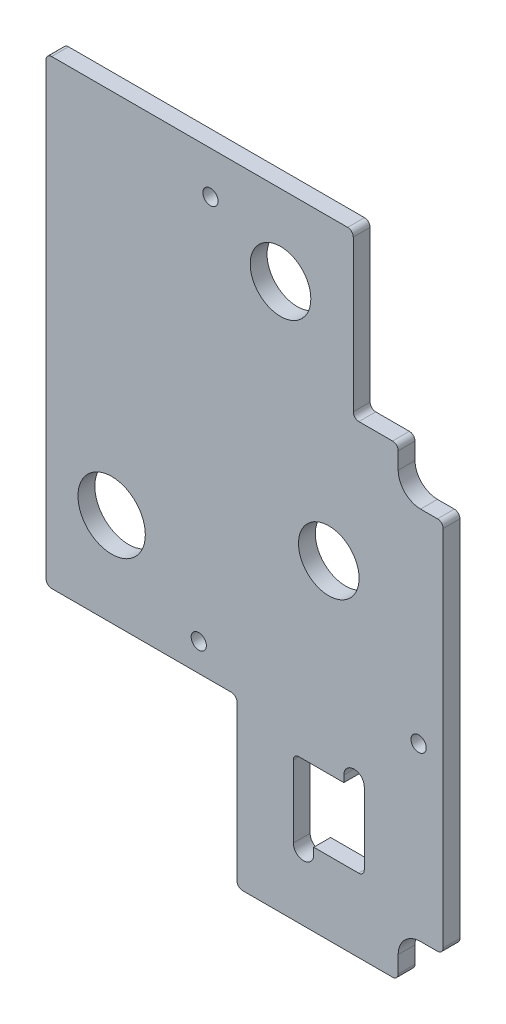
SolidWorks part; units mm, degrees
ref_plane "Front Plane" through (0, 0, 0) normal (0, 0, 1) x (1, 0, 0)
ref_plane "Top Plane" through (0, 0, 0) normal (0, 1, 0) x (1, 0, 0)
ref_plane "Right Plane" through (0, 0, 0) normal (1, 0, 0) x (0, 0, -1)
sketch "Sketch3" plane through (0, 0, 0) normal (0, 0, 1) x (1, 0, 0)
  line L8 (13.7795, -148.717) -> (13.7795, -168.783)
  line L9 (33.8455, -148.717) -> (13.7795, -148.717)
  line L10 (33.8455, -168.783) -> (33.8455, -148.717)
  line L11 (13.7795, -168.783) -> (33.8455, -168.783)
  line L12 (-0.5715, -189.484) -> (41.8465, -189.484)
  line L13 (43.434, -187.8965) -> (43.434, -183.134)
  line L14 (49.784, -176.784) -> (54.5465, -176.784)
  line L15 (56.134, -175.1965) -> (56.134, -72.4535)
  line L16 (54.5465, -70.866) -> (49.784, -70.866)
  line L17 (43.434, -64.516) -> (43.434, -59.7535)
  line L18 (41.8465, -58.166) -> (32.3215, -58.166)
  line L19 (30.734, -56.5785) -> (30.734, -13.7795)
  line L20 (29.1465, -12.192) -> (-54.5465, -12.192)
  line L21 (-56.134, -13.7795) -> (-56.134, -140.9065)
  line L22 (-54.5465, -142.494) -> (-3.7465, -142.494)
  line L23 (-2.159, -144.0815) -> (-2.159, -187.8965)
  line L24 (-0.5715, -189.484) -> (41.8465, -189.484)
  line L25 (43.434, -187.8965) -> (43.434, -183.134)
  line L26 (49.784, -176.784) -> (54.5465, -176.784)
  line L27 (56.134, -175.1965) -> (56.134, -72.4535)
  line L28 (54.5465, -70.866) -> (49.784, -70.866)
  line L29 (43.434, -64.516) -> (43.434, -59.7535)
  line L30 (41.8465, -58.166) -> (32.3215, -58.166)
  line L31 (30.734, -56.5785) -> (30.734, -13.7795)
  line L32 (29.1465, -12.192) -> (-54.5465, -12.192)
  line L33 (-56.134, -13.7795) -> (-56.134, -140.9065)
  line L34 (-54.5465, -142.494) -> (-3.7465, -142.494)
  line L35 (-2.159, -144.0815) -> (-2.159, -187.8965)
  arc A12 (-2.159, -187.8965) -> (-0.5715, -189.484) centre (-0.5715, -187.8965) ccw
  arc A13 (-2.159, -187.8965) -> (-0.5715, -189.484) centre (-0.5715, -187.8965) ccw
  arc A14 (41.8465, -189.484) -> (43.434, -187.8965) centre (41.8465, -187.8965) ccw
  arc A15 (41.8465, -189.484) -> (43.434, -187.8965) centre (41.8465, -187.8965) ccw
  arc A16 (49.784, -176.784) -> (43.434, -183.134) centre (49.784, -183.134) ccw
  arc A17 (49.784, -176.784) -> (43.434, -183.134) centre (49.784, -183.134) ccw
  arc A18 (54.5465, -176.784) -> (56.134, -175.1965) centre (54.5465, -175.1965) ccw
  arc A19 (54.5465, -176.784) -> (56.134, -175.1965) centre (54.5465, -175.1965) ccw
  arc A20 (56.134, -72.4535) -> (54.5465, -70.866) centre (54.5465, -72.4535) ccw
  arc A21 (56.134, -72.4535) -> (54.5465, -70.866) centre (54.5465, -72.4535) ccw
  arc A22 (43.434, -64.516) -> (49.784, -70.866) centre (49.784, -64.516) ccw
  arc A23 (43.434, -64.516) -> (49.784, -70.866) centre (49.784, -64.516) ccw
  arc A24 (43.434, -59.7535) -> (41.8465, -58.166) centre (41.8465, -59.7535) ccw
  arc A25 (43.434, -59.7535) -> (41.8465, -58.166) centre (41.8465, -59.7535) ccw
  arc A26 (30.734, -56.5785) -> (32.3215, -58.166) centre (32.3215, -56.5785) ccw
  arc A27 (30.734, -56.5785) -> (32.3215, -58.166) centre (32.3215, -56.5785) ccw
  arc A28 (30.734, -13.7795) -> (29.1465, -12.192) centre (29.1465, -13.7795) ccw
  arc A29 (30.734, -13.7795) -> (29.1465, -12.192) centre (29.1465, -13.7795) ccw
  arc A30 (-54.5465, -12.192) -> (-56.134, -13.7795) centre (-54.5465, -13.7795) ccw
  arc A31 (-54.5465, -12.192) -> (-56.134, -13.7795) centre (-54.5465, -13.7795) ccw
  arc A32 (-56.134, -140.9065) -> (-54.5465, -142.494) centre (-54.5465, -140.9065) ccw
  arc A33 (-56.134, -140.9065) -> (-54.5465, -142.494) centre (-54.5465, -140.9065) ccw
  arc A34 (-2.159, -144.0815) -> (-3.7465, -142.494) centre (-3.7465, -144.0815) ccw
  arc A35 (-2.159, -144.0815) -> (-3.7465, -142.494) centre (-3.7465, -144.0815) ccw
  dimension "D1" = 0
extrude "Boss-Extrude1" add sketch "Sketch3" along normal blind 4.7625
sketch "Sketch6" plane through (161.4861, -518.0111, 4.7625) normal (0, 0, 1) x (1, 0, 0)
  circle A0 centre (-137.6736, 421.4911) radius 8.5725
  dimension "D1" = 17.145
extrude "Cut-Extrude4" cut sketch "Sketch6" against normal through all
other "Smart-Feature1<SxAL-1>"
sketch "Sketch61" plane through (147.8336, -456.4161, 4.7625) normal (0, 0, 1) x (1, 0, 0)
  circle A0 centre (-137.6736, 421.4911) radius 8.5725
  dimension "D1" = 17.145
extrude "Cut-Extrude41" cut sketch "Sketch61" against normal through all
other "Smart-Feature2<SxAL-2>"
sketch "Sketch62" plane through (0, 0, 4.7625) normal (0, 0, 1) x (1, 0, 0)
  circle A0 centre (-37.592, -116.078) radius 9.525
  dimension "D1" = 19.05
extrude "Cut-Extrude42" cut sketch "Sketch62" against normal through all
hole_wizard "#6 Clearance Hole1" positions "Sketch63" profile "Sketch64" hole size "#6" standard "ANSI Inch" end condition through all
sketch "Sketch63" plane through (36.5125, -265.1125, 6.35) normal (0, 0, 1) x (-1, 0, 0)
  point P0 (49.4665, -130.4925)
  point P3 (-12.7, -136.525)
  point P6 (46.1645, -240.9825)
sketch "Sketch64" plane through (-12.954, -134.62, 6.35) normal (1, 0, 0) x (0, -1, 0)
  line L0 (0, 0) -> (0, 6.35)
  line L1 (0, 6.35) -> (2.1526, 6.35)
  line L2 (2.1526, 6.35) -> (2.1526, 0)
  line L3 (2.1526, 0) -> (0, 0)
  line L4 (0, -6.35) -> (0, 107.95) construction
  dimension "Thru Hole Dia." = 4.3053
  dimension "Thru Hole Depth" = 6.35
sketch "Sketch67" plane through (0, 0, 0) normal (0, 0, -1) x (-1, 0, 0)
  line L0 (-16.6688, -170.6563) -> (-16.6688, -167.4813) construction
  line L1 (-19.558, -170.6563) -> (-19.558, -167.4813)
  line L2 (-13.7795, -170.6563) -> (-13.7795, -167.4813)
  line L3 (-30.9563, -146.8438) -> (-30.9563, -150.0188) construction
  line L4 (-28.067, -146.8438) -> (-28.067, -150.0188)
  line L5 (-33.8455, -146.8438) -> (-33.8455, -150.0188)
  line L6 (-13.7795, -148.717) -> (-13.7795, -168.783) construction
  arc A0 (-19.558, -170.6563) -> (-13.7795, -170.6563) centre (-16.6688, -170.6563) ccw
  arc A1 (-13.7795, -167.4813) -> (-19.558, -167.4813) centre (-16.6688, -167.4813) ccw
  arc A2 (-28.067, -146.8438) -> (-33.8455, -146.8438) centre (-30.9563, -146.8438) ccw
  arc A3 (-33.8455, -150.0188) -> (-28.067, -150.0188) centre (-30.9563, -150.0188) ccw
  point P2 (-16.6688, -169.0688)
  point P7 (-30.9563, -148.4313)
  dimension "D2" = 3.175
extrude "Cut-Extrude43" cut sketch "Sketch67" against normal up to next contours L1 A1 L2 A0 | A3 L4 A2 L5
fillet "Fillet1" radius 1.5875 2 edges at (13.7795, -148.717, 2.3813) (33.8455, -168.783, 2.3813)
